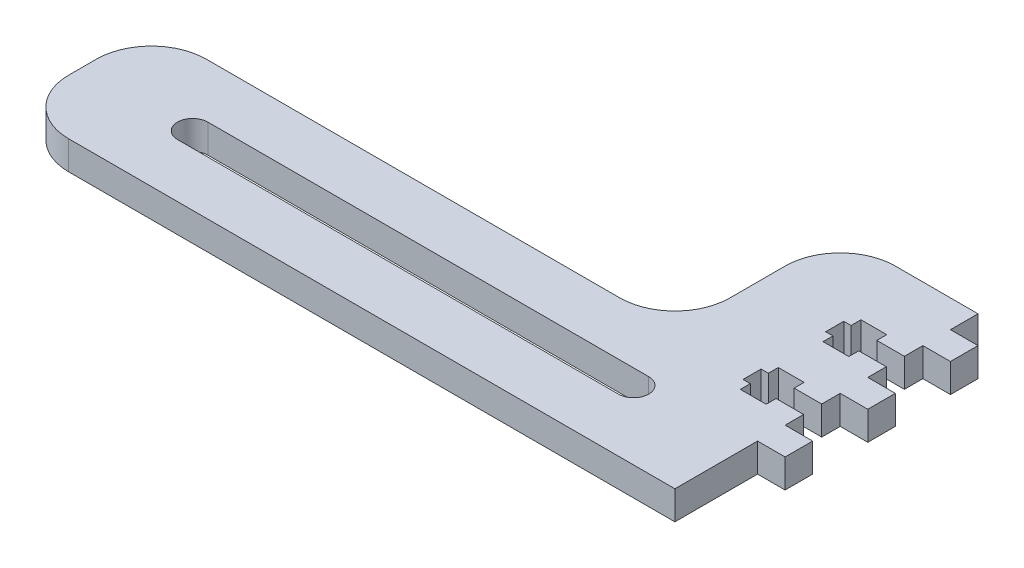
SolidWorks part; units mm, degrees
material "Acrylic (BLUE)"
ref_plane "Front Plane" through (0, 0, 0) normal (0, 0, 1) x (1, 0, 0)
ref_plane "Top Plane" through (0, 0, 0) normal (0, 1, 0) x (1, 0, 0)
ref_plane "Right Plane" through (0, 0, 0) normal (1, 0, 0) x (0, 0, -1)
sketch "Sketch1" plane through (0, 0, 0) normal (0, 1, 0) x (1, 0, 0)
  line L0 (-152.4, -38.1) -> (-152.4, -69.85)
  line L3 (-152.4, -69.85) -> (0, -69.85)
  line L4 (0, 0) -> (0, -69.85)
  line L6 (0, 0) -> (-31.75, 0)
  line L7 (-152.4, -38.1) -> (-31.75, -38.1)
  line L8 (-31.75, 0) -> (-31.75, -38.1)
  dimension "D1" = 69.85
  dimension "D2" = 152.4
  dimension "D3" = 31.75
  dimension "D4" = 31.75
extrude "Boss-Extrude1" add sketch "Sketch1" along normal blind 6.604
fillet "Fillet1" radius 12.7 4 edges at (-152.4, 3.302, 69.85) (-152.4, 3.302, 38.1) (-31.75, 3.302, 38.1) (-31.75, 3.302, 0)
sketch "Sketch2" plane through (0, 6.604, 0) normal (0, 1, 0) x (1, 0, 0)
  line L0 (-152.4, -50.8) -> (-152.4, -57.15) construction
  line L1 (0, -69.85) -> (0, 0) construction
  line L6 (-127, -53.975) -> (-25.4, -53.975) construction
  line L7 (-127, -57.4675) -> (-25.4, -57.4675)
  line L8 (-127, -50.4825) -> (-25.4, -50.4825)
  arc A2 (-127, -57.4675) -> (-127, -50.4825) centre (-127, -53.975) cw
  arc A3 (-25.4, -50.4825) -> (-25.4, -57.4675) centre (-25.4, -53.975) cw
  point P17 (-76.2, -53.975)
  point P22 (-152.4, -53.975)
  dimension "D3" = 6.985
  dimension "D1" = 25.4
  dimension "D2" = 25.4
extrude "Cut-Extrude1" cut sketch "Sketch2" against normal up to next
sketch "Sketch3" plane through (0, 6.604, 0) normal (0, 1, 0) x (1, 0, 0)
  line L0 (0, -69.85) -> (0, 0) construction
  line L1 (0, 0) -> (-19.05, 0) construction
  line B0 (0, -16.9672) -> (-6.35, -16.9672)
  line B1 (-6.35, -16.9672) -> (-6.35, -14.6812)
  line B2 (-6.35, -14.6812) -> (-12.2936, -14.6812)
  line B3 (-12.2936, -14.6812) -> (-12.2936, -16.9672)
  line B4 (-12.2936, -16.9672) -> (-13.97, -16.9672)
  line B5 (-13.97, -16.9672) -> (-13.97, -21.1328)
  line B6 (-13.97, -21.1328) -> (-12.2936, -21.1328)
  line B7 (-12.2936, -21.1328) -> (-12.2936, -23.4188)
  line B8 (-12.2936, -23.4188) -> (-6.35, -23.4188)
  line B9 (-6.35, -23.4188) -> (-6.35, -21.1328)
  line B10 (-6.35, -21.1328) -> (0, -21.1328)
  line B11 (0, -25.4) -> (6.35, -25.4)
  line B12 (6.35, -25.4) -> (6.35, -31.75)
  line B13 (6.35, -31.75) -> (0, -31.75)
  line B14 (0, -16.9672) -> (0, -12.7)
  line B15 (0, -12.7) -> (6.35, -12.7)
  line B16 (6.35, -12.7) -> (6.35, -6.35)
  line B17 (6.35, -6.35) -> (0, -6.35)
  line B18 (0, -21.1328) -> (0, -16.9672) construction
  line B19 (6.35, -50.8) -> (0, -50.8)
  line B20 (0, -36.0172) -> (-6.35, -36.0172)
  line B21 (-6.35, -36.0172) -> (-6.35, -33.7312)
  line B22 (-6.35, -33.7312) -> (-12.2936, -33.7312)
  line B23 (-12.2936, -33.7312) -> (-12.2936, -36.0172)
  line B24 (-12.2936, -36.0172) -> (-13.97, -36.0172)
  line B25 (-13.97, -36.0172) -> (-13.97, -40.1828)
  line B26 (-13.97, -40.1828) -> (-12.2936, -40.1828)
  line B27 (-12.2936, -40.1828) -> (-12.2936, -42.4688)
  line B28 (-12.2936, -42.4688) -> (-6.35, -42.4688)
  line B29 (-6.35, -42.4688) -> (-6.35, -40.1828)
  line B30 (-6.35, -40.1828) -> (0, -40.1828)
  line B31 (0, -40.1828) -> (0, -44.45)
  line B32 (0, -44.45) -> (6.35, -44.45)
  line B33 (6.35, -44.45) -> (6.35, -50.8)
  line B34 (0, -36.0172) -> (0, -31.75)
  line B35 (0, -40.1828) -> (0, -36.0172) construction
  dimension "D1" = 6.35
sketch_block_instance "NUT_HOLE_2X-1"
sketch_block "NUT_HOLE_2X" parameters "D1"=6.35, "D2"=4.1656, "D3"=25.4, "D4"=6.35, "D5"=8.7376, "D6"=5.9436, "D7"=6.35, "D8"=20.32, "D9"=2
sketch "Sketch4" plane through (0, 6.604, 0) normal (0, 1, 0) x (1, 0, 0)
  line L0 (0, -16.9672) -> (-6.35, -16.9672) construction
  line L1 (-6.35, -21.1328) -> (0, -21.1328) construction
  line L2 (0, -36.0172) -> (-6.35, -36.0172) construction
  line L3 (-6.35, -40.1828) -> (0, -40.1828) construction
  line L4 (-6.35, -42.4688) -> (-6.35, -40.1828) construction
  line L5 (-12.2936, -42.4688) -> (-6.35, -42.4688) construction
  line L6 (-12.2936, -40.1828) -> (-12.2936, -42.4688) construction
  line L7 (-13.97, -40.1828) -> (-12.2936, -40.1828) construction
  line L8 (-13.97, -36.0172) -> (-13.97, -40.1828) construction
  line L9 (-12.2936, -36.0172) -> (-13.97, -36.0172) construction
  line L10 (-12.2936, -33.7312) -> (-12.2936, -36.0172) construction
  line L11 (-6.35, -33.7312) -> (-12.2936, -33.7312) construction
  line L12 (-6.35, -36.0172) -> (-6.35, -33.7312) construction
  line L13 (-6.35, -23.4188) -> (-6.35, -21.1328) construction
  line L14 (-12.2936, -23.4188) -> (-6.35, -23.4188) construction
  line L15 (-12.2936, -21.1328) -> (-12.2936, -23.4188) construction
  line L16 (-13.97, -21.1328) -> (-12.2936, -21.1328) construction
  line L17 (-13.97, -16.9672) -> (-13.97, -21.1328) construction
  line L18 (-12.2936, -16.9672) -> (-13.97, -16.9672) construction
  line L19 (-6.35, -14.6812) -> (-12.2936, -14.6812) construction
  line L20 (-12.2936, -14.6812) -> (-12.2936, -16.9672) construction
  line L21 (-6.35, -16.9672) -> (-6.35, -14.6812) construction
  line L22 (0, -16.9672) -> (-6.35, -16.9672)
  line L23 (-6.35, -21.1328) -> (0, -21.1328)
  line L24 (0, -36.0172) -> (-6.35, -36.0172)
  line L25 (-6.35, -40.1828) -> (0, -40.1828)
  line L26 (-6.35, -42.4688) -> (-6.35, -40.1828)
  line L27 (-12.2936, -42.4688) -> (-6.35, -42.4688)
  line L28 (-12.2936, -40.1828) -> (-12.2936, -42.4688)
  line L29 (-13.97, -40.1828) -> (-12.2936, -40.1828)
  line L30 (-13.97, -36.0172) -> (-13.97, -40.1828)
  line L31 (-12.2936, -36.0172) -> (-13.97, -36.0172)
  line L32 (-12.2936, -33.7312) -> (-12.2936, -36.0172)
  line L33 (-6.35, -33.7312) -> (-12.2936, -33.7312)
  line L34 (-6.35, -36.0172) -> (-6.35, -33.7312)
  line L35 (-6.35, -23.4188) -> (-6.35, -21.1328)
  line L36 (-12.2936, -23.4188) -> (-6.35, -23.4188)
  line L37 (-12.2936, -21.1328) -> (-12.2936, -23.4188)
  line L38 (-13.97, -21.1328) -> (-12.2936, -21.1328)
  line L39 (-13.97, -16.9672) -> (-13.97, -21.1328)
  line L40 (-12.2936, -16.9672) -> (-13.97, -16.9672)
  line L41 (-6.35, -14.6812) -> (-12.2936, -14.6812)
  line L42 (-12.2936, -14.6812) -> (-12.2936, -16.9672)
  line L43 (-6.35, -16.9672) -> (-6.35, -14.6812)
  line L44 (0, -16.9672) -> (0, -21.1328)
  line L45 (0, -36.0172) -> (0, -40.1828)
extrude "Cut-Extrude2" cut sketch "Sketch4" against normal through all
sketch "Sketch5" plane through (0, 6.604, 0) normal (0, 1, 0) x (1, 0, 0)
  line L0 (6.35, -6.35) -> (0, -6.35) construction
  line L1 (6.35, -12.7) -> (6.35, -6.35) construction
  line L2 (0, -12.7) -> (6.35, -12.7) construction
  line L3 (0, -25.4) -> (6.35, -25.4) construction
  line L4 (6.35, -25.4) -> (6.35, -31.75) construction
  line L5 (6.35, -31.75) -> (0, -31.75) construction
  line L6 (0, -44.45) -> (6.35, -44.45) construction
  line L7 (6.35, -44.45) -> (6.35, -50.8) construction
  line L8 (6.35, -50.8) -> (0, -50.8) construction
  line L9 (6.35, -6.35) -> (0, -6.35)
  line L10 (6.35, -12.7) -> (6.35, -6.35)
  line L11 (0, -12.7) -> (6.35, -12.7)
  line L12 (0, -25.4) -> (6.35, -25.4)
  line L13 (6.35, -25.4) -> (6.35, -31.75)
  line L14 (6.35, -31.75) -> (0, -31.75)
  line L15 (0, -44.45) -> (6.35, -44.45)
  line L16 (6.35, -44.45) -> (6.35, -50.8)
  line L17 (6.35, -50.8) -> (0, -50.8)
  line L18 (0, -6.35) -> (0, -12.7)
  line L20 (0, -25.4) -> (0, -31.75)
  line L21 (0, -44.45) -> (0, -50.8)
extrude "Boss-Extrude2" add sketch "Sketch5" against normal up to surface (6.604 mm away) up to face at (-76.2, 0, 53.975)
other "Move Face1" [suppressed] parameters "D1"=0.0508
